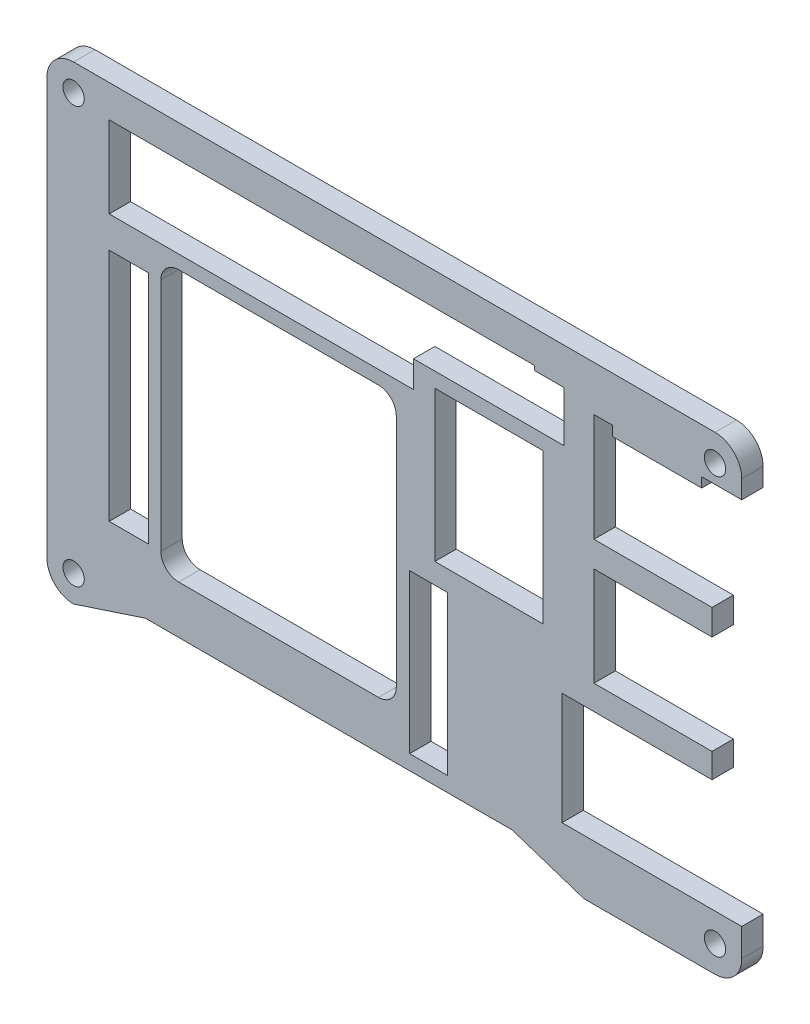
SolidWorks part; units mm, degrees
ref_plane "Front Plane" through (0, 0, 0) normal (0, 0, 1) x (1, 0, 0)
ref_plane "Top Plane" through (0, 0, 0) normal (0, 1, 0) x (1, 0, 0)
ref_plane "Right Plane" through (0, 0, 0) normal (1, 0, 0) x (0, 0, -1)
sketch "Sketch1" plane through (0, 0, 0) normal (0, 0, 1) x (1, 0, 0)
  line L3 (56.975, 4.9979) -> (56.975, 8.6582) construction
  line L7 (56.975, -12.628) -> (56.975, -9.1218) construction
  line L8 (35.575, -12.628) -> (56.975, -12.628) construction
  line L9 (35.575, -28.6278) -> (35.575, -12.628) construction
  line L10 (61.2149, -28.6278) -> (35.575, -28.6278) construction
  line L11 (61.2149, -32.6134) -> (61.2149, -28.6278) construction
  line L12 (38.7143, -36.451) -> (57.405, -36.451) construction
  line L13 (28.4743, -33.0844) -> (38.7143, -36.451) construction
  line L14 (61.2149, 24.0683) -> (61.2149, 26.6839) construction
  line L15 (61.2149, 24.0683) -> (40.1348, 24.0683)
  line L16 (40.1348, 24.0683) -> (40.1348, 8.6582)
  line L17 (40.1348, 8.6582) -> (56.975, 8.6582)
  line L18 (56.975, 4.9979) -> (56.975, 8.6582)
  line L19 (56.975, 4.9979) -> (40.1348, 4.9979)
  line L20 (40.1348, 4.9979) -> (40.1348, -9.1218)
  line L21 (40.1348, -9.1218) -> (56.975, -9.1218)
  line L22 (56.975, -12.628) -> (56.975, -9.1218)
  line L23 (35.575, -12.628) -> (56.975, -12.628)
  line L24 (35.575, -28.6278) -> (35.575, -12.628)
  line L25 (61.2149, -28.6278) -> (35.575, -28.6278)
  line L26 (61.2149, -32.6134) -> (61.2149, -28.6278)
  line L27 (38.7143, -36.451) -> (57.405, -36.451)
  line L28 (28.4743, -33.0844) -> (38.7143, -36.451)
  line L29 (61.2149, 24.0683) -> (61.2149, 26.6839)
  line L30 (57.4049, 30.5077) -> (-34.0849, 30.5077) construction
  line L31 (-37.8949, 26.6977) -> (-37.8949, -32.641) construction
  line L32 (-34.0849, -36.451) -> (-23.8449, -33.0844) construction
  line L33 (57.4049, 30.5077) -> (-34.0849, 30.5077)
  line L34 (-37.8949, 26.6977) -> (-37.8949, -32.641)
  line L35 (-34.0849, -36.451) -> (-23.8449, -33.0844)
  line L36 (-23.8449, -33.0844) -> (28.4743, -33.0844)
  line L40 (13.845, -30.9668) -> (13.845, -8.3602)
  line L41 (13.845, -8.3602) -> (19.2484, -8.3602)
  line L42 (19.2484, -8.3602) -> (19.2484, -30.9668)
  line L43 (19.2484, -30.9668) -> (13.845, -30.9668)
  line L45 (-29.0049, 25.897) -> (31.6883, 25.897)
  line L46 (-29.0049, 25.897) -> (-29.0049, 18.087)
  line L47 (-29.0049, 18.087) -> (31.6883, 18.087)
  line L48 (31.6883, 25.897) -> (31.6883, 18.087)
  line L49 (17.441, 15.9724) -> (32.872, 15.9724)
  line L50 (17.441, 15.9724) -> (17.441, -5.4315)
  line L51 (17.441, -5.4315) -> (32.872, -5.4315)
  line L52 (32.872, 15.9724) -> (32.872, -5.4315)
  line L53 (-21.6389, 10.5941) -> (10.329, 10.5941)
  line L54 (-21.6389, 10.5941) -> (-21.6389, -7.643)
  line L55 (-21.6389, -7.643) -> (10.329, -7.643)
  line L56 (10.329, 10.5941) -> (10.329, -7.643)
  line L57 (-23.4169, 9.8012) -> (-29.0049, 9.8012)
  line L58 (-23.4169, 9.8012) -> (-23.4169, -23.6989)
  line L59 (-23.4169, -23.6989) -> (-29.0049, -23.6989)
  line L60 (-29.0049, 9.8012) -> (-29.0049, -23.6989)
  arc A0 (57.405, -36.451) -> (61.2149, -32.6134) centre (57.405, -32.641) ccw construction
  arc A1 (61.2149, 26.6839) -> (57.4049, 30.5077) centre (57.4049, 26.6977) ccw construction
  circle A2 centre (57.4049, 26.6977) radius 1.3462 construction
  circle A3 centre (57.405, -32.641) radius 1.3462 construction
  circle A4 centre (-34.0849, -32.641) radius 1.3462 construction
  circle A5 centre (-34.0849, 26.6977) radius 1.3462 construction
  arc A6 (57.405, -36.451) -> (61.2149, -32.6134) centre (57.405, -32.641) ccw
  arc A7 (61.2149, 26.6839) -> (57.4049, 30.5077) centre (57.4049, 26.6977) ccw
  circle A8 centre (57.4049, 26.6977) radius 1.3462
  circle A9 centre (57.405, -32.641) radius 1.3462
  circle A10 centre (-34.0849, -32.641) radius 1.3462
  circle A11 centre (-34.0849, 26.6977) radius 1.3462
  arc A12 (-34.0849, 30.5077) -> (-37.8949, 26.6977) centre (-34.0849, 26.6977) ccw construction
  arc A13 (-37.8949, -32.641) -> (-34.0849, -36.451) centre (-34.0849, -32.641) ccw construction
  arc A14 (-34.0849, 30.5077) -> (-37.8949, 26.6977) centre (-34.0849, 26.6977) ccw
  arc A15 (-37.8949, -32.641) -> (-34.0849, -36.451) centre (-34.0849, -32.641) ccw
  dimension "D1" = 16.8402
  dimension "D2" = 16.8402
extrude "Boss-Extrude1" add sketch "Sketch1" along normal blind 3.048
sketch "Sketch2" plane through (0, 0, 3.048) normal (0, 0, 1) x (1, 0, 0)
  line L0 (-21.6389, 10.5941) -> (-21.6389, -7.643) construction
  line L1 (11.94, 12.3412) -> (-21.6389, 12.3412)
  line L2 (11.94, 12.3412) -> (11.94, -26.2389)
  line L3 (11.94, -26.2389) -> (-21.6389, -26.2389)
  line L4 (-21.6389, 12.3412) -> (-21.6389, -26.2389)
  line L6 (-23.4169, 9.8012) -> (-29.0049, 9.8012) construction
  line L9 (-29.0049, -23.6989) -> (-23.4169, -23.6989) construction
  line L10 (13.845, -8.3602) -> (13.845, -30.9668) construction
  dimension "D1" = 2.54
  dimension "D2" = 2.54
  dimension "D3" = 1.905
extrude "Cut-Extrude1" cut sketch "Sketch2" against normal through all
fillet "Fillet1" radius 2.54 4 edges at (11.94, -26.2389, 1.524) (-21.6389, -26.2389, 1.524) (-21.6389, 12.3412, 1.524) (11.94, 12.3412, 1.524)
sketch "Sketch3" plane through (0, 0, 3.048) normal (0, 0, 1) x (1, 0, 0)
  circle A0 centre (-34.0849, 26.6977) radius 1.524
  circle A1 centre (57.4049, 26.6977) radius 1.524
  circle A2 centre (57.405, -32.641) radius 1.524
  circle A3 centre (-34.0849, -32.641) radius 1.524
  dimension "D1" = 3.048
extrude "Cut-Extrude2" cut sketch "Sketch3" against normal through all
sketch "Sketch4" plane through (0, 0, 3.048) normal (0, 0, 1) x (1, 0, 0)
  line L1 (14.393, 18.087) -> (-29.0049, 18.087)
  line L2 (14.393, 18.087) -> (14.393, 14.277)
  line L3 (14.393, 14.277) -> (-29.0049, 14.277)
  line L4 (-29.0049, 18.087) -> (-29.0049, 14.277)
  line L5 (17.441, 15.9724) -> (17.441, -5.4315) construction
  dimension "D1" = 3.81
  dimension "D2" = 3.048
extrude "Cut-Extrude3" cut sketch "Sketch4" against normal through all
sketch "Sketch5" plane through (0, 0, 3.048) normal (0, 0, 1) x (1, 0, 0)
  line L0 (40.1348, 24.0683) -> (61.2149, 24.0683) construction
  line L1 (55.4999, 24.0683) -> (42.7999, 24.0683)
  line L2 (55.4999, 24.0683) -> (55.4999, 22.6713)
  line L3 (55.4999, 22.6713) -> (42.7999, 22.6713)
  line L4 (42.7999, 24.0683) -> (42.7999, 22.6713)
  line L5 (61.2149, 24.0683) -> (61.2149, 26.6839) construction
  dimension "D1" = 1.397
  dimension "D2" = 12.7
  dimension "D3" = 5.715
extrude "Boss-Extrude2" add sketch "Sketch5" against normal blind 3.048
sketch "Sketch6" plane through (0, 0, 3.048) normal (0, 0, 1) x (1, 0, 0)
  line L1 (35.88, 25.262) -> (31.6883, 25.262)
  line L2 (35.88, 25.262) -> (35.88, 18.087)
  line L3 (35.88, 18.087) -> (31.6883, 18.087)
  line L4 (31.6883, 25.262) -> (31.6883, 18.087)
  dimension "D1" = 4.1917
  dimension "D2" = 7.175
extrude "Cut-Extrude4" cut sketch "Sketch6" against normal through all
